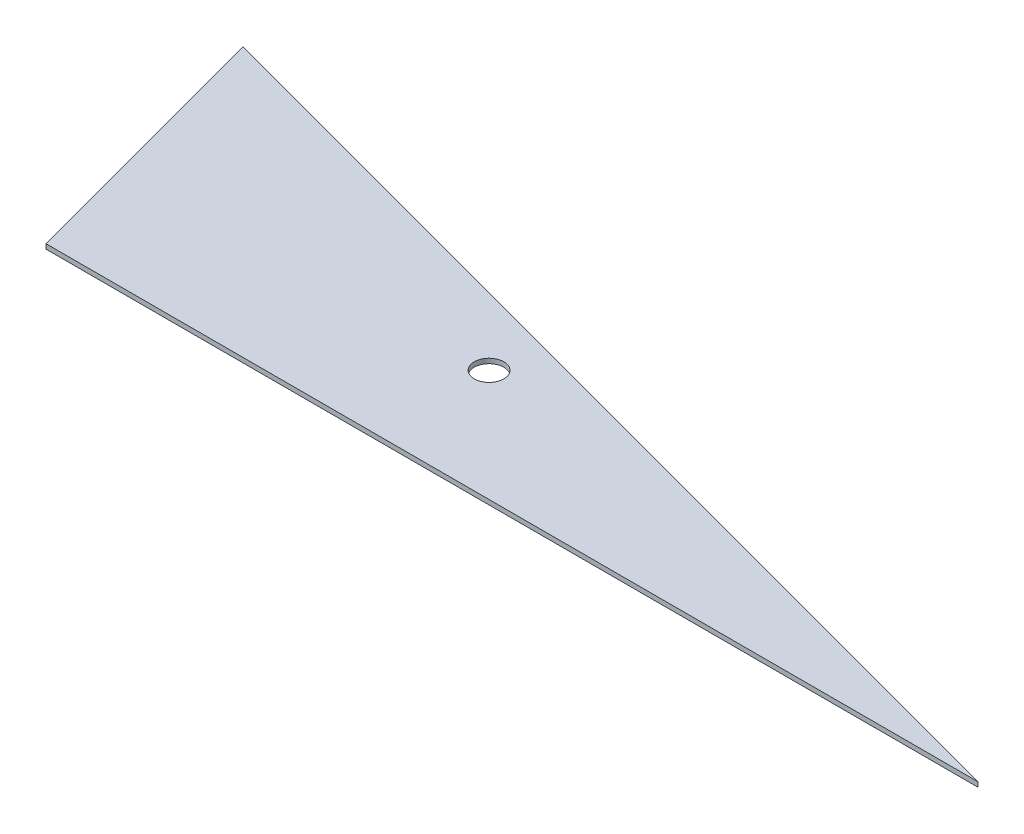
SolidWorks part; units mm, degrees
ref_plane "Front Plane" through (0, 0, 0) normal (0, 0, 1) x (1, 0, 0)
ref_plane "Top Plane" through (0, 0, 0) normal (0, 1, 0) x (1, 0, 0)
ref_plane "Right Plane" through (0, 0, 0) normal (1, 0, 0) x (0, 0, -1)
sketch "Sketch1" plane through (0, 0, 0) normal (0, 1, 0) x (1, 0, 0)
  line L0 (-288.6359, -221.3841) -> (-288.6359, -365.4205)
  line L1 (-288.6359, -365.4205) -> (248.9154, -365.4205)
  line L2 (248.9154, -365.4205) -> (-288.6359, -221.3841)
  dimension "D1" = 556.514
  dimension "D2" = 15
extrude "Boss-Extrude1" add sketch "Sketch1" along normal blind 2.54
sketch "Sketch2" plane through (0, 2.54, 0) normal (0, 1, 0) x (1, 0, 0)
  line L0 (-288.6359, -221.3841) -> (-288.6359, -365.4205) construction
  line L1 (248.9154, -365.4205) -> (-288.6359, -221.3841) construction
  circle A0 centre (-72.7359, -305.5303) radius 7.9375
  dimension "D1" = 215.9
  dimension "D2" = 15.875
  dimension "D3" = 25.4
extrude "Cut-Extrude1" cut sketch "Sketch2" against normal blind 2.54
sketch "Sketch3" plane through (0, 0, 0) normal (0, -1, 0) x (1, 0, 0)
  line L0 (-288.6359, 221.3841) -> (-250.0414, 365.4205)
  line L1 (-288.6359, 365.4205) -> (248.9154, 365.4205) construction
  line L2 (-250.0414, 365.4205) -> (-288.6359, 365.4205)
  line L3 (-288.6359, 365.4205) -> (-288.6359, 221.3841)
  point P5 (0, 0)
  dimension "D1" = 15
extrude "Cut-Extrude2" cut sketch "Sketch3" against normal blind 2.54
